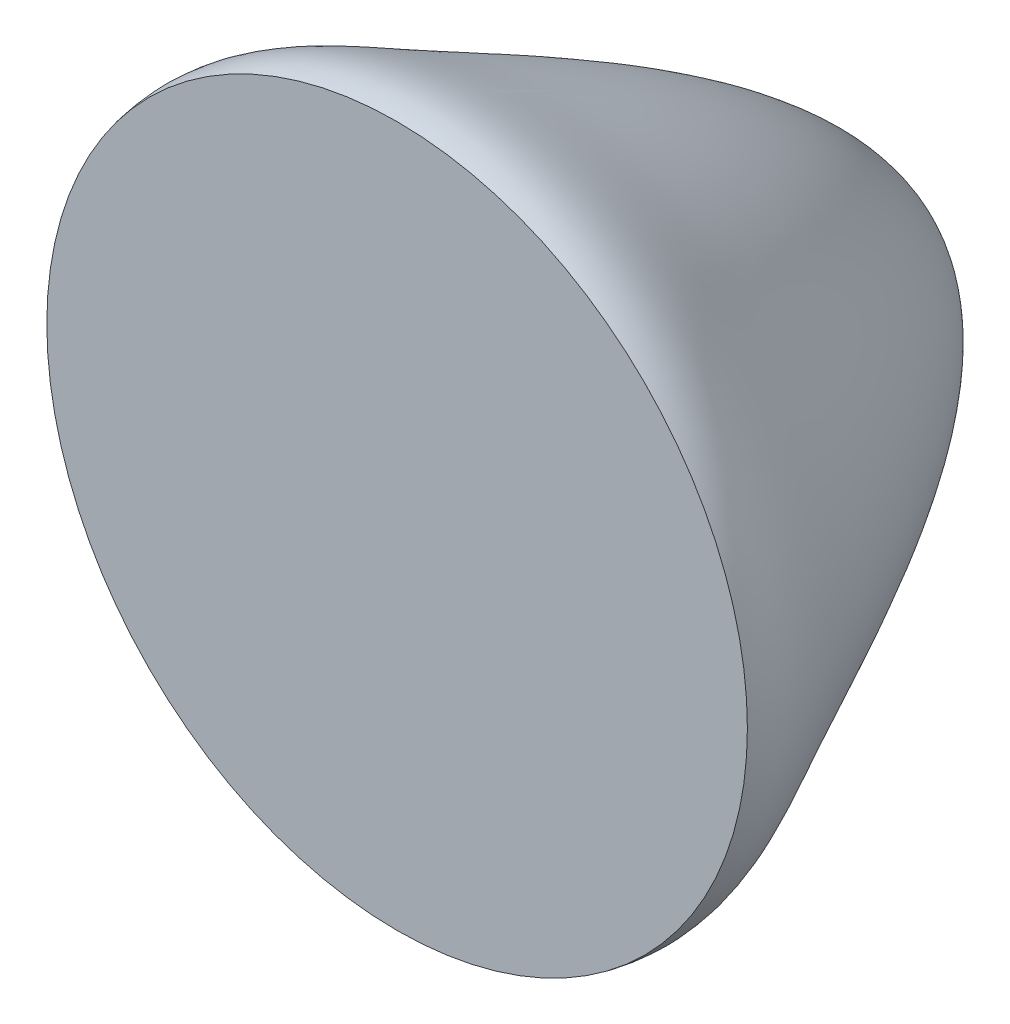
SolidWorks part; units mm, degrees
ref_plane "Front Plane" through (0, 0, 0) normal (0, 0, 1) x (1, 0, 0)
ref_plane "Top Plane" through (0, 0, 0) normal (0, 1, 0) x (1, 0, 0)
ref_plane "Right Plane" through (0, 0, 0) normal (1, 0, 0) x (0, 0, -1)
sketch "Sketch2" plane through (0, 0, 0) normal (1, 0, 0) x (0, 0, -1)
  line L0 (0, 0.8) -> (0, 0)
  line L1 (1.15, 0) -> (0, 0)
  line L2 (0, 0.8) -> (-0.4087, 0.7116) construction
  line L3 (1.15, 0) -> (1.15, -0.272) construction
  spline S0 degree 3 poles (0, 0.8) (0.0989, 0.8214) (0.3217, 0.6796) (1.15, 0.3197) (1.15, 0) knots 0 0 0 0 0.365919 1 1 1 1
  dimension "D1" = 0.8
  dimension "D2" = 1.15
revolve "Revolve1" add sketch "Sketch2" angle 360 about L1
